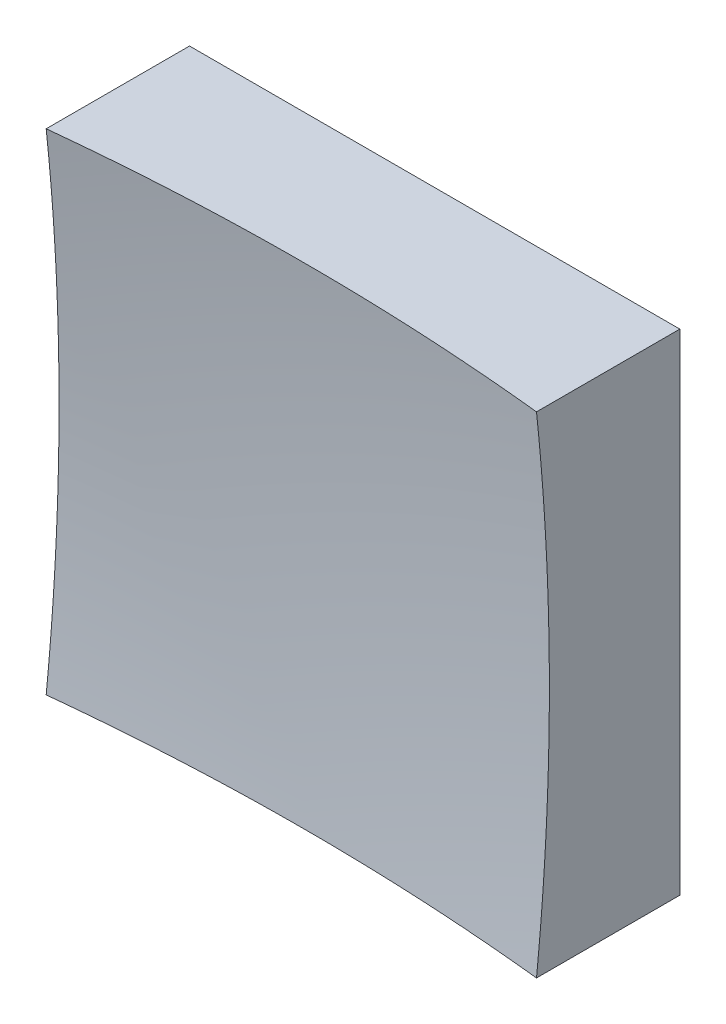
SolidWorks part; units mm, degrees
ref_plane "前视基准面" through (0, 0, 0) normal (0, 0, 1) x (1, 0, 0)
ref_plane "上视基准面" through (0, 0, 0) normal (0, 1, 0) x (1, 0, 0)
ref_plane "右视基准面" through (0, 0, 0) normal (1, 0, 0) x (0, 0, -1)
sketch "草图1" plane through (0, 0, 0) normal (0, 0, 1) x (1, 0, 0)
  line L1 (-6.25, 6.25) -> (6.25, 6.25)
  line L2 (-6.25, 6.25) -> (-6.25, -6.25)
  line L3 (-6.25, -6.25) -> (6.25, -6.25)
  line L4 (6.25, 6.25) -> (6.25, -6.25)
  line L5 (-6.25, 6.25) -> (6.25, -6.25) construction
  line L6 (-6.25, -6.25) -> (6.25, 6.25) construction
  point P0 (0, 0)
  dimension "D1" = 12.5
  dimension "D2" = 12.5
extrude "凸台-拉伸1" add sketch "草图1" along normal blind 10 contours L2 L3 L4 L1
sketch "草图2" plane through (0, 0, 0) normal (0, 1, 0) x (1, 0, 0)
  line L0 (-7.4603, -3) -> (7.3192, -3) construction
  line L1 (0, 0) -> (0, -12.1749) construction
  line L2 (58.4907, -49.6271) -> (0, -49.6271)
  line L3 (0, -49.6271) -> (0, -3)
  arc A1 (58.4907, -49.6271) -> (0, -3) centre (0, -63) ccw
  dimension "D2" = 120
  dimension "D1" = 3
revolve "切除-旋转2" cut sketch "草图2" angle 360 about L3
